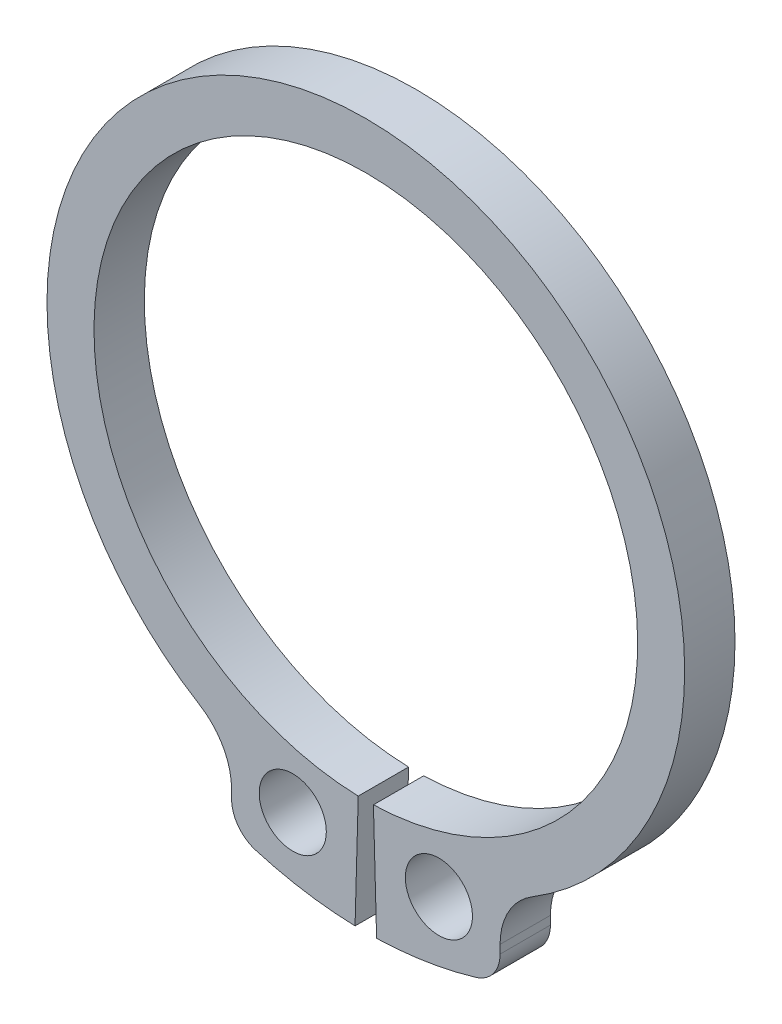
SolidWorks part; units mm, degrees
material "ABS"
ref_plane "Спереди" through (0, 0, 0) normal (0, 0, 1) x (1, 0, 0)
ref_plane "Сверху" through (0, 0, 0) normal (0, 1, 0) x (1, 0, 0)
ref_plane "Справа" through (0, 0, 0) normal (1, 0, 0) x (0, 0, -1)
sketch "Эскиз1" plane through (0, 0, 0) normal (0, 0, 1) x (1, 0, 0)
  line L0 (0, -9.6776) -> (0, 50000) construction
  line L1 (0, 0) -> (-0.1961, -7.0212) construction
  line L2 (-0.3211, -11.4955) -> (-0.2262, -8.0968)
  line L3 (-0.2262, -8.0968) -> (-0.8681, -31.0788) construction
  line L4 (-4, -10.0623) -> (-4, -9.8107)
  line L5 (4, -10.0623) -> (4, -9.8107)
  line L6 (0.3211, -11.4955) -> (0.2262, -8.0968)
  arc A0 (0.2262, -8.0968) -> (-0.2262, -8.0968) centre (0, 0) ccw
  circle A2 centre (0, 0) radius 12 construction
  circle A3 centre (0, 0) radius 8.5 construction
  arc A4 (-3.2857, -11.0206) -> (-0.3211, -11.4955) centre (0, 0) ccw
  arc A5 (-4, -9.8107) -> (-4.9565, -8.1045) centre (-6, -9.8107) ccw
  arc A6 (-3.2857, -11.0206) -> (-4, -10.0623) centre (-3, -10.0623) cw
  arc A7 (3.2857, -11.0206) -> (4, -10.0623) centre (3, -10.0623) ccw
  arc A8 (4, -9.8107) -> (4.9565, -8.1045) centre (6, -9.8107) cw
  arc A9 (0.3211, -11.4955) -> (3.2857, -11.0206) centre (0, 0) ccw
  arc A10 (4.9565, -8.1045) -> (-4.9565, -8.1045) centre (0, 0) ccw
  circle A11 centre (-2.0907, -9.6776) radius 0.996
  circle A12 centre (2.0907, -9.6776) radius 0.996
  dimension "D1" = 16.2
  dimension "D3" = 24
  dimension "D4" = 17
  dimension "D6" = 23
  dimension "D8" = 2
  dimension "D9" = 1
  dimension "D5" = 1.6
  dimension "D7" = 8
extrude "Бобышка-Вытянуть1" add sketch "Эскиз1" along normal blind 1.5 contours A10 A5 L4 A6 A4 L2 A0 L6 A9 A7 L5 A8
sketch "Эскиз2" plane through (0, 0, 0) normal (0, 0, -1) x (-1, 0, 0)
  line L0 (0, 0) -> (0, -23.8017) construction
  circle A0 centre (-2.177, -9.4946) radius 1
  circle A1 centre (2.177, -9.4946) radius 1
  dimension "D1" = 2
extrude "Вырез-Вытянуть1" cut sketch "Эскиз2" against normal blind 1.5
